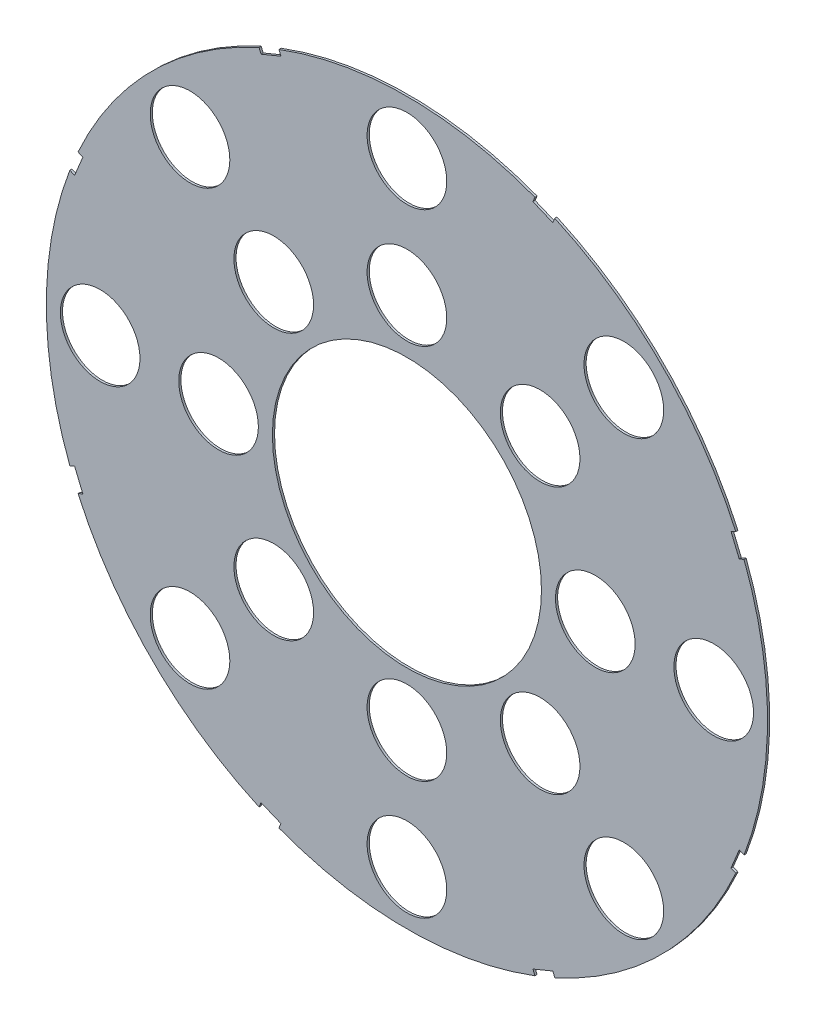
SolidWorks part; units mm, degrees
material "PTFE (general)"
ref_plane "Front Plane" through (0, 0, 0) normal (0, 0, 1) x (1, 0, 0)
ref_plane "Top Plane" through (0, 0, 0) normal (0, 1, 0) x (1, 0, 0)
ref_plane "Right Plane" through (0, 0, 0) normal (1, 0, 0) x (0, 0, -1)
sketch "Sketch4" plane through (0, 0, 0) normal (0, 0, 1) x (1, 0, 0)
  circle A0 centre (0, 0) radius 42.545
  dimension "D1" = 85.09
extrude "Boss-Extrude2" add sketch "Sketch4" along normal blind 0.254
sketch "Sketch5" plane through (0, 0, 0.254) normal (0, 0, 1) x (1, 0, 0)
  circle A0 centre (0, 0) radius 15.875
  dimension "D1" = 31.75
extrude "Cut-Extrude5" cut sketch "Sketch5" against normal through all
sketch "Sketch8" plane through (0, 0, 0.254) normal (0, 0, 1) x (1, 0, 0)
  line L2 (40.3791, 15.3509) -> (39.4071, 17.6976)
  line L3 (40.3791, 15.3509) -> (39.2058, 14.8649)
  line L4 (39.2058, 14.8649) -> (38.2338, 17.2116)
  line L5 (39.4071, 17.6976) -> (38.2338, 17.2116)
  line L6 (0, 0) -> (42.545, 0) construction
  line L7 (-15.3509, 40.3791) -> (-17.6976, 39.4071)
  line L8 (-15.3509, 40.3791) -> (-14.8649, 39.2058)
  line L9 (-17.6976, 39.4071) -> (-17.2116, 38.2338)
  line L10 (-14.8649, 39.2058) -> (-17.2116, 38.2338)
  line L11 (-17.6976, 39.4071) -> (-14.8649, 39.2058) construction
  line L12 (-15.3509, 40.3791) -> (-17.2116, 38.2338) construction
  line L13 (-39.4071, 17.6976) -> (-40.3791, 15.3509)
  line L14 (-39.4071, 17.6976) -> (-38.2338, 17.2116)
  line L15 (-38.2338, 17.2116) -> (-39.2058, 14.8649)
  line L16 (-40.3791, 15.3509) -> (-39.2058, 14.8649)
  line L17 (-39.4071, 17.6976) -> (-39.2058, 14.8649) construction
  line L18 (-40.3791, 15.3509) -> (-38.2338, 17.2116) construction
  line L19 (-40.3791, -15.3509) -> (-39.4071, -17.6976)
  line L20 (-40.3791, -15.3509) -> (-39.2058, -14.8649)
  line L21 (-39.2058, -14.8649) -> (-38.2338, -17.2116)
  line L22 (-39.4071, -17.6976) -> (-38.2338, -17.2116)
  line L23 (-40.3791, -15.3509) -> (-38.2338, -17.2116) construction
  line L24 (-39.4071, -17.6976) -> (-39.2058, -14.8649) construction
  line L25 (-17.6976, -39.4071) -> (-15.3509, -40.3791)
  line L26 (-17.6976, -39.4071) -> (-17.2116, -38.2338)
  line L27 (-17.2116, -38.2338) -> (-14.8649, -39.2058)
  line L28 (-15.3509, -40.3791) -> (-14.8649, -39.2058)
  line L29 (-17.6976, -39.4071) -> (-14.8649, -39.2058) construction
  line L30 (-15.3509, -40.3791) -> (-17.2116, -38.2338) construction
  line L31 (15.3509, -40.3791) -> (17.6976, -39.4071)
  line L32 (15.3509, -40.3791) -> (14.8649, -39.2058)
  line L33 (14.8649, -39.2058) -> (17.2116, -38.2338)
  line L34 (17.6976, -39.4071) -> (17.2116, -38.2338)
  line L35 (15.3509, -40.3791) -> (17.2116, -38.2338) construction
  line L36 (17.6976, -39.4071) -> (14.8649, -39.2058) construction
  line L37 (39.4071, -17.6976) -> (40.3791, -15.3509)
  line L38 (39.4071, -17.6976) -> (38.2338, -17.2116)
  line L39 (38.2338, -17.2116) -> (39.2058, -14.8649)
  line L40 (40.3791, -15.3509) -> (39.2058, -14.8649)
  line L41 (39.4071, -17.6976) -> (39.2058, -14.8649) construction
  line L42 (40.3791, -15.3509) -> (38.2338, -17.2116) construction
  line L43 (40.3791, 15.3509) -> (38.2338, 17.2116) construction
  line L44 (39.4071, 17.6976) -> (39.2058, 14.8649) construction
  line L45 (17.6976, 39.4071) -> (15.3509, 40.3791)
  line L46 (17.6976, 39.4071) -> (17.2116, 38.2338)
  line L47 (17.2116, 38.2338) -> (14.8649, 39.2058)
  line L48 (15.3509, 40.3791) -> (14.8649, 39.2058)
  line L49 (17.6976, 39.4071) -> (14.8649, 39.2058) construction
  line L50 (15.3509, 40.3791) -> (17.2116, 38.2338) construction
  circle A0 centre (0, 0) radius 42.545 construction
  point P3 (-16.2813, 39.3065)
  point P11 (-39.3065, 16.2813)
  point P15 (39.3065, 16.2813)
  point P20 (-39.3065, -16.2813)
  point P25 (-16.2813, -39.3065)
  point P26 (0, 0)
  point P31 (16.2813, -39.3065)
  point P36 (39.3065, -16.2813)
  point P45 (16.2813, 39.3065)
  point P46 (0, 0)
  dimension "D3" = 0.635
  dimension "D5" = 1.27
  dimension "D6" = 2.54
  dimension "D7" = 1.27
  dimension "D9" = 0.635
  dimension "D10" = 112.5
  dimension "D14" = 0.635
  dimension "D21" = 22.5
  dimension "D11" = 8
extrude "Cut-Extrude11" cut sketch "Sketch8" against normal through all
sketch "Sketch9" plane through (0, 0, 0.254) normal (0, 0, 1) x (1, 0, 0)
  line L0 (0, 0) -> (36.195, 0) construction
  line L1 (0, 0) -> (25.5937, 25.5937) construction
  line L2 (0, 0) -> (25.5937, -25.5937) construction
  circle A0 centre (22.225, 0) radius 4.699
  circle A1 centre (36.195, 0) radius 4.699
  circle A4 centre (0, 0) radius 15.875 construction
  circle A6 centre (15.7154, -15.7154) radius 4.699
  circle A7 centre (25.5937, -25.5937) radius 4.699
  circle A10 centre (0, -22.225) radius 4.699
  circle A11 centre (0, -36.195) radius 4.699
  circle A14 centre (-15.7154, -15.7154) radius 4.699
  circle A15 centre (-25.5937, -25.5937) radius 4.699
  circle A18 centre (-22.225, 0) radius 4.699
  circle A19 centre (-36.195, 0) radius 4.699
  circle A22 centre (-15.7154, 15.7154) radius 4.699
  circle A23 centre (-25.5937, 25.5937) radius 4.699
  circle A26 centre (0, 22.225) radius 4.699
  circle A27 centre (0, 36.195) radius 4.699
  circle A30 centre (15.7154, 15.7154) radius 4.699
  circle A31 centre (25.5937, 25.5937) radius 4.699
  point P2 (0, 0)
  point P4 (0, 0)
  point P5 (0, 0)
  point P74 (0, 0)
  point P87 (0, 0)
  dimension "D1" = 13.97
  dimension "D2" = 9.398
  dimension "D4" = 6.35
  dimension "D8" = 45
  dimension "D9" = 45
  dimension "D7" = 8
extrude "Cut-Extrude12" cut sketch "Sketch9" against normal through all
equation "\"CoilSep\"= 1.005"
